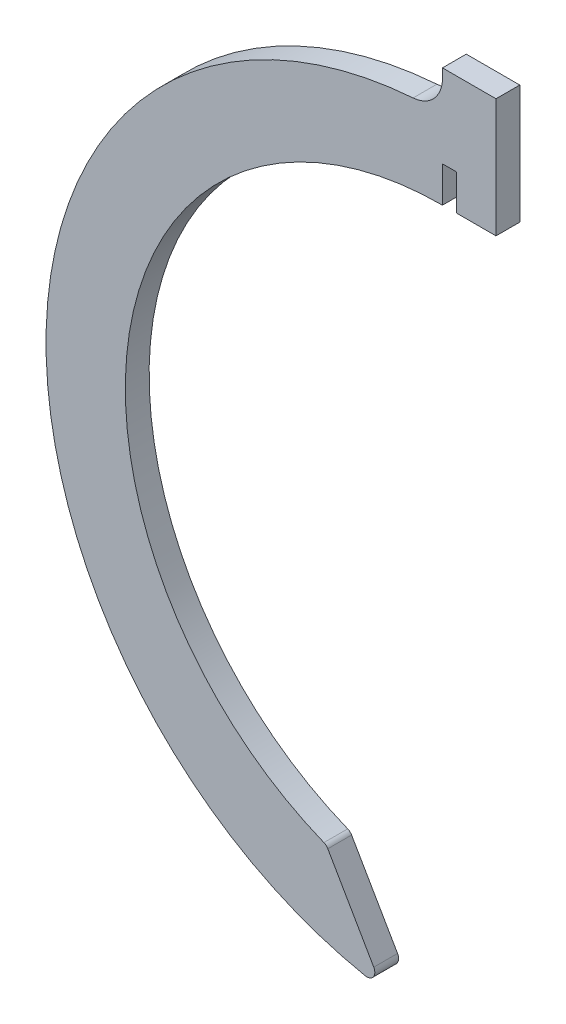
SolidWorks part; units mm, degrees
ref_plane "Front Plane" through (0, 0, 0) normal (0, 0, 1) x (1, 0, 0)
ref_plane "Top Plane" through (0, 0, 0) normal (0, 1, 0) x (1, 0, 0)
ref_plane "Right Plane" through (0, 0, 0) normal (1, 0, 0) x (0, 0, -1)
sketch "Sketch1" plane through (0, 0, 0) normal (0, 0, 1) x (1, 0, 0)
  line L0 (-14.6354, -37.2264) -> (-7.5956, -49.4197)
  line L1 (0, -49.4197) -> (0, -50) construction
  line L2 (-7.5956, -49.4197) -> (-74.1062, -49.4197) construction
  line L3 (-74.1062, -49.4197) -> (0, -49.4197) construction
  line L4 (-74.1062, -34.4197) -> (0, -34.4197) construction
  line L5 (0, -49.4197) -> (0, -50)
  line L6 (36.9347, -34.4197) -> (92.3772, -34.4197) construction
  line L16 (0, 50) -> (6.75, 50)
  line L17 (0, 40) -> (0, 44.5184)
  line L18 (0, 44.5184) -> (1.79, 44.5184)
  line L19 (1.79, 44.5184) -> (1.79, 40.02)
  line L20 (1.79, 40.02) -> (6.75, 40.02)
  line L21 (6.75, 40.02) -> (6.75, 50)
  line L23 (0, 50) -> (6.75, 50)
  line L24 (0, 50) -> (0, 55)
  line L25 (0, 55) -> (6.75, 55)
  line L26 (6.75, 50) -> (6.75, 55)
  arc A0 (0, 40) -> (-14.6354, -37.2264) centre (0, 0) ccw
  arc A1 (0, 50) -> (-7.5956, -49.4197) centre (0, 0) ccw
  dimension "D1" = 80
  dimension "D2" = 10
  dimension "D3" = 15
  dimension "D4" = 60
  dimension "D5" = 6.75
  dimension "D6" = 1.79
  dimension "D7" = 9.98
  dimension "D8" = 4.96
  dimension "D9" = 5
extrude "Boss-Extrude1" add sketch "Sketch1" along normal blind 3 contours L16 L26 L25 L24 | L16 A1 L0 A0 L17 L18 L19 L20 L21
fillet "Fillet3" radius 1 1 edges at (-7.5956, -49.4197, 1.5)
fillet "Fillet4" radius 1 1 edges at (-14.6354, -37.2264, 1.5)
fillet "Fillet6" radius 4 1 edges at (0, 50, 1.5)
